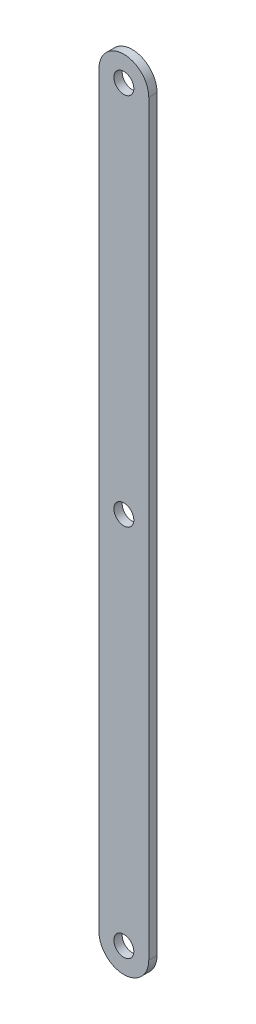
SolidWorks part; units mm, degrees
ref_plane "前视基准面" through (0, 0, 0) normal (0, 0, 1) x (1, 0, 0)
ref_plane "上视基准面" through (0, 0, 0) normal (0, 1, 0) x (1, 0, 0)
ref_plane "右视基准面" through (0, 0, 0) normal (1, 0, 0) x (0, 0, -1)
sketch "草图1" plane through (0, 0, 0) normal (0, 0, 1) x (1, 0, 0)
  line L1 (8.3631, 62.6958) -> (8.3631, 512.6958)
  line L3 (38.3631, 512.6958) -> (38.3631, 62.6958)
  line L4 (38.3631, 62.6958) -> (8.3631, 62.6958) construction
  line L6 (23.3631, 512.6958) -> (23.3631, 62.6958) construction
  line L7 (23.3631, 512.6958) -> (23.3631, 287.6958) construction
  circle A0 centre (23.3631, 512.6958) radius 6
  arc A1 (38.3631, 512.6958) -> (8.3631, 512.6958) centre (23.3631, 512.6958) ccw
  circle A2 centre (23.3631, 62.6958) radius 6
  arc A4 (8.3631, 62.6958) -> (38.3631, 62.6958) centre (23.3631, 62.6958) ccw
  circle A5 centre (23.3631, 287.6958) radius 6
  dimension "D2" = 450
  dimension "D4" = 12
  dimension "D5" = 12
  dimension "D1" = 12
  dimension "D3" = 30
extrude "凸台-拉伸1" add sketch "草图1" along normal blind 5
